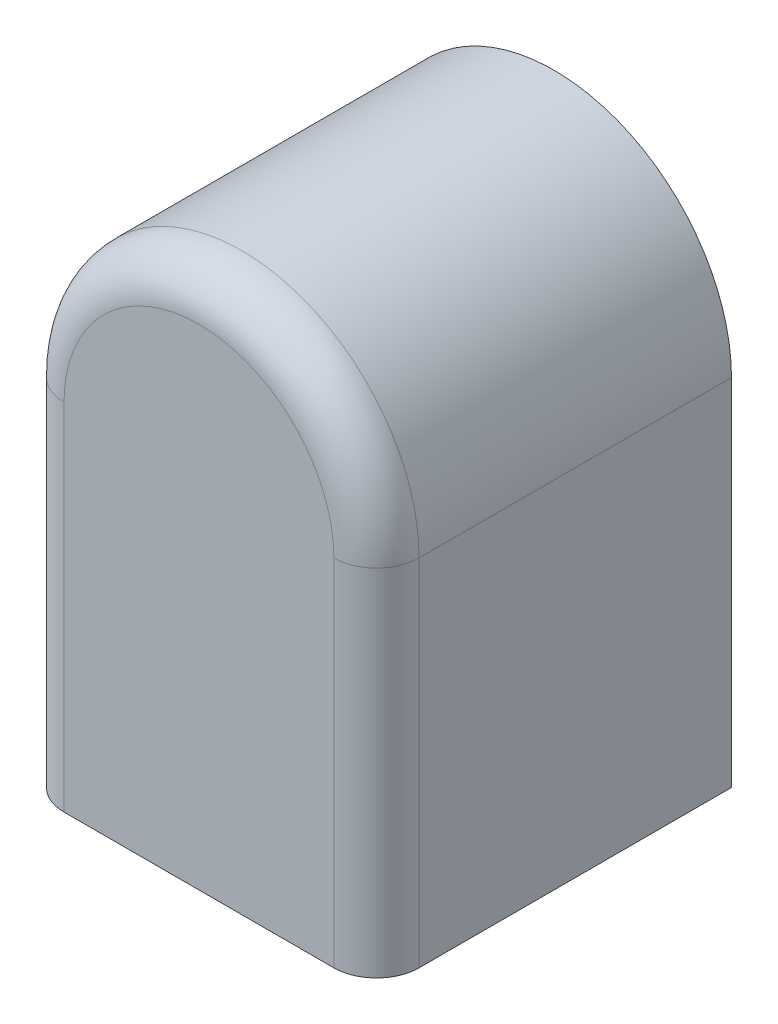
SolidWorks part; units mm, degrees
ref_plane "Спереди" through (0, 0, 0) normal (0, 0, 1) x (1, 0, 0)
ref_plane "Сверху" through (0, 0, 0) normal (0, 1, 0) x (1, 0, 0)
ref_plane "Справа" through (0, 0, 0) normal (1, 0, 0) x (0, 0, -1)
sketch "Эскиз1" plane through (0, 0, 0) normal (0, 0, 1) x (1, 0, 0)
  line L0 (-12.5, 0) -> (-12.5, -25)
  line L1 (-12.5, -25) -> (12.5, -25)
  line L2 (12.5, -25) -> (12.5, 0)
  arc A0 (12.5, 0) -> (-12.5, 0) centre (0, 0) ccw
  dimension "D1" = 25
  dimension "D2" = 25
extrude "Бобышка-Вытянуть1" add sketch "Эскиз1" along normal blind 25
fillet "Скругление1" radius 3 3 edges at (12.5, -12.5, 25) (-12.5, -12.5, 25) (0, 12.5, 25)
